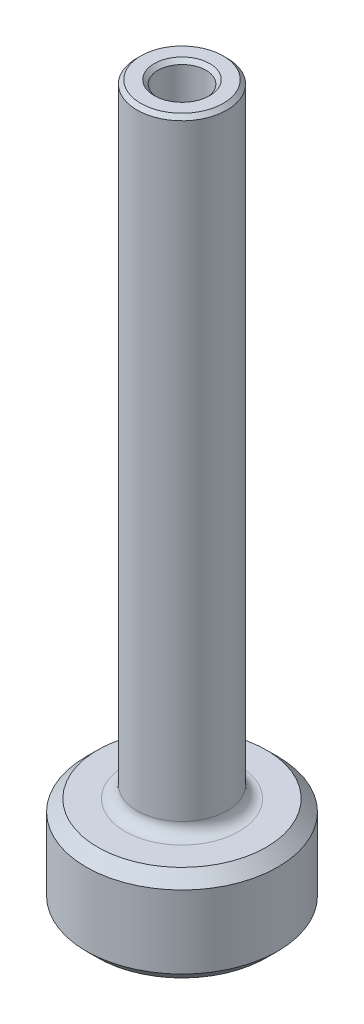
SolidWorks part; units mm, degrees
ref_plane "Front" through (0, 0, 0) normal (0, 0, 1) x (1, 0, 0)
ref_plane "Top" through (0, 0, 0) normal (0, 1, 0) x (1, 0, 0)
ref_plane "Right" through (0, 0, 0) normal (1, 0, 0) x (0, 0, -1)
sketch "Sketch1" plane through (0, 0, 0) normal (0, 0, 1) x (1, 0, 0)
  line L0 (0, 5.5693) -> (0, -5.1628) construction
  line L1 (3.175, 0) -> (6.35, 0)
  line L2 (6.35, 0) -> (6.35, 6.35)
  line L3 (6.35, 6.35) -> (2.9845, 6.35)
  line L4 (2.9845, 6.35) -> (2.9845, 47.625)
  line L5 (2.9845, 47.625) -> (1.5875, 47.625)
  line L6 (1.5875, 47.625) -> (1.5875, 3.175)
  line L7 (1.5875, 3.175) -> (3.175, 3.175)
  line L8 (3.175, 3.175) -> (3.175, 0)
  dimension "D1" = 12.7
  dimension "D2" = 5.969
  dimension "D3" = 3.175
  dimension "D4" = 6.35
  dimension "D5" = 3.175
  dimension "D6" = 3.175
  dimension "D7" = 41.275
revolve "Revolve1" add sketch "Sketch1" angle 360 about L0
sketch "Sketch2" plane through (0, 0, 0) normal (0, -1, 0) x (1, 0, 0)
  line L1 (1.8331, 3.175) -> (-1.8331, 3.175)
  line L2 (-1.8331, 3.175) -> (-3.6662, 0)
  line L3 (-3.6662, 0) -> (-1.8331, -3.175)
  line L4 (-1.8331, -3.175) -> (1.8331, -3.175)
  line L5 (1.8331, -3.175) -> (3.6662, 0)
  line L6 (3.6662, 0) -> (1.8331, 3.175)
  circle A0 centre (0, 0) radius 3.175 construction
  circle A1 centre (0, 0) radius 3.175 construction
extrude "Cut-Extrude1" cut sketch "Sketch2" against normal up to surface (3.175 mm away) up to face at (-3.175, 3.175, 0)
fillet "Fillet1" radius 0.7937 13 edges at (0, 3.175, 3.175) (2.7496, 3.175, 1.5875) (2.7496, 3.175, -1.5875) (0, 3.175, -3.175) (-2.7496, 3.175, -1.5875) (-2.7496, 3.175, 1.5875) (-1.8331, 1.5875, 3.175) (1.8331, 1.5875, 3.175) (3.6662, 1.5875, 0) (1.8331, 1.5875, -3.175) (-1.8331, 1.5875, -3.175) (-3.6662, 1.5875, 0) (-2.9845, 6.35, 0)
chamfer "Chamfer1" distance 0.254 angle 45 15 edges at (-1.5875, 3.175, 0) (-1.5875, 47.625, 0) (-2.9845, 47.625, 0) (0, 0, -3.175) (1.7717, 0, -3.0687) (-1.7717, 0, -3.0687) (2.7496, 0, -1.5875) (-2.7496, 0, -1.5875) (3.5434, 0, 0) (-3.5434, 0, 0) (2.7496, 0, 1.5875) (-2.7496, 0, 1.5875) (1.7717, 0, 3.0687) (-1.7717, 0, 3.0687) (0, 0, 3.175)
chamfer "Chamfer2" distance 0.762 angle 45 2 edges at (-6.35, 0, 0) (-6.35, 6.35, 0)
